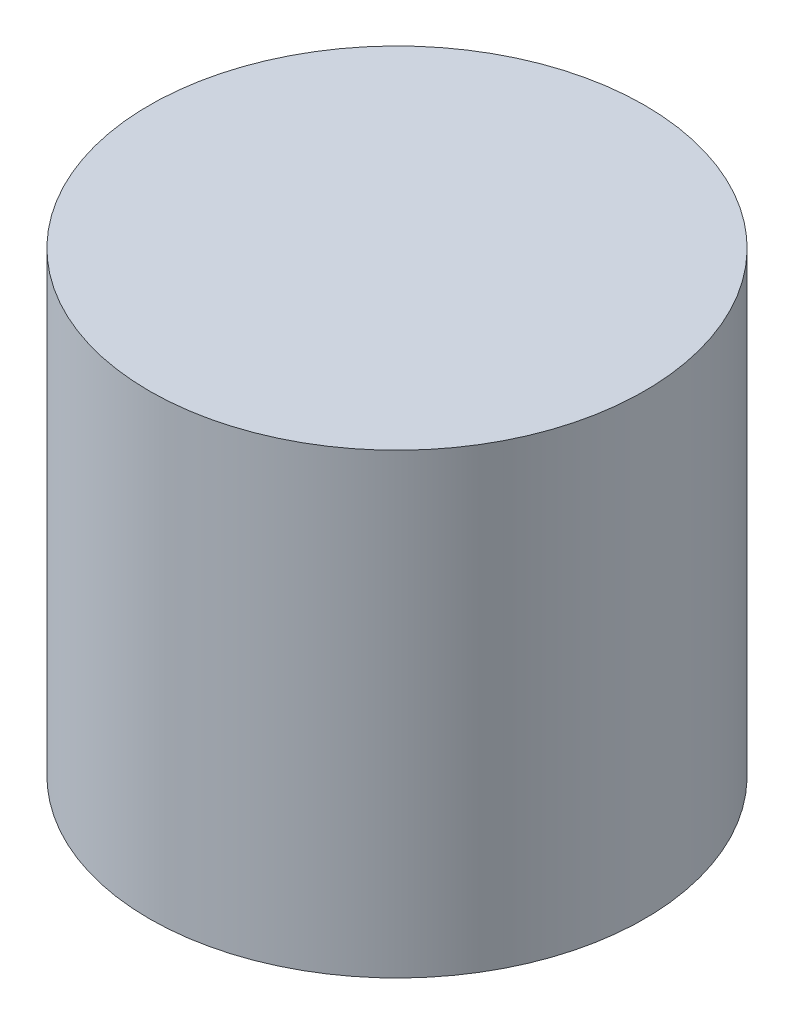
SolidWorks part; units mm, degrees
material "Custom Plastic"
ref_plane "Front Plane" through (0, 0, 0) normal (0, 0, 1) x (1, 0, 0)
ref_plane "Top Plane" through (0, 0, 0) normal (0, 1, 0) x (1, 0, 0)
ref_plane "Right Plane" through (0, 0, 0) normal (1, 0, 0) x (0, 0, -1)
sketch "Sketch1" plane through (0, 0, 0) normal (0, 1, 0) x (1, 0, 0)
  circle A0 centre (0, 0) radius 6.35
  circle A1 centre (0, 0) radius 8.255
  dimension "D1" = 12.7
  dimension "D2" = 16.51
extrude "Boss-Extrude1" add sketch "Sketch1" along normal blind 12.7
sketch "Sketch2" plane through (0, 12.7, 0) normal (0, 1, 0) x (1, 0, 0)
  circle A0 centre (0, 0) radius 8.255
  circle A1 centre (0, 0) radius 8.255 construction
extrude "Boss-Extrude2" add sketch "Sketch2" along normal blind 2.54
chamfer "Chamfer1" distance 0.508 angle 45 1 edges at (0, 0, 6.35)
